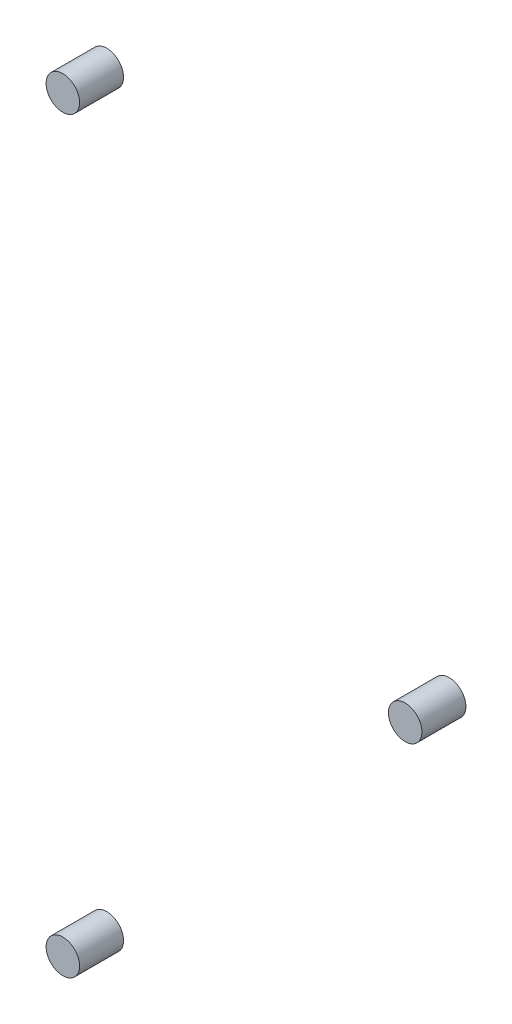
SolidWorks part; units mm, degrees
ref_plane "前视基准面" through (0, 0, 0) normal (0, 0, 1) x (1, 0, 0)
ref_plane "上视基准面" through (0, 0, 0) normal (0, 1, 0) x (1, 0, 0)
ref_plane "右视基准面" through (0, 0, 0) normal (1, 0, 0) x (0, 0, -1)
sketch "草图1" plane through (0, 0, 0) normal (0, 0, 1) x (1, 0, 0)
  circle A0 centre (37.8499, 34.0208) radius 1.525 construction
  circle A1 centre (69, 0) radius 1.525 construction
  circle A2 centre (37.8499, -34.0208) radius 1.525 construction
  circle A3 centre (37.8499, 34.0208) radius 1.525
  circle A4 centre (69, 0) radius 1.525
  circle A5 centre (37.8499, -34.0208) radius 1.525
extrude "凸台-拉伸1" add sketch "草图1" along normal blind 4
